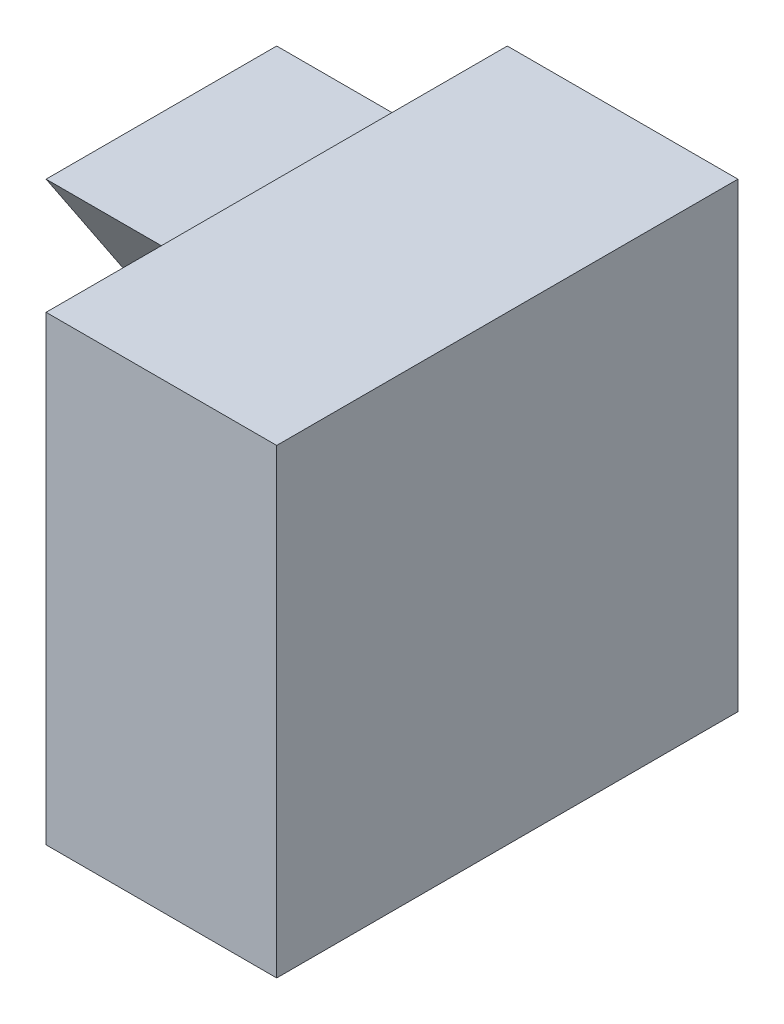
SolidWorks part; units mm, degrees
ref_plane "Front Plane" through (0, 0, 0) normal (0, 0, 1) x (1, 0, 0)
ref_plane "Top Plane" through (0, 0, 0) normal (0, 1, 0) x (1, 0, 0)
ref_plane "Right Plane" through (0, 0, 0) normal (1, 0, 0) x (0, 0, -1)
sketch "Sketch1" plane through (0, 0, 0) normal (1, 0, 0) x (0, 0, -1)
  line L1 (0, 0) -> (4, 0)
  line L2 (0, 0) -> (0, 4)
  line L3 (0, 4) -> (4, 4)
  line L4 (4, 0) -> (4, 4)
  dimension "D1" = 4
  dimension "D2" = 4
extrude "Boss-Extrude1" add sketch "Sketch1" along normal blind 2
sketch "Sketch2" plane through (0, 0, 0) normal (-1, 0, 0) x (0, 0, 1)
  line L1 (-4, 0) -> (-2, 0)
  line L2 (-4, 0) -> (-4, 3)
  line L3 (-4, 3) -> (-2, 3)
  line L4 (-2, 0) -> (-2, 3)
  dimension "D1" = 3
  dimension "D2" = 2
extrude "Boss-Extrude2" add sketch "Sketch2" along normal blind 2
sketch "Sketch3" plane through (-2, 0, 0) normal (-1, 0, 0) x (0, 0, 1)
  line L0 (-2, 3) -> (-4, 0)
  line L1 (-4, 0) -> (-2, 0)
  line L2 (-2, 0) -> (-2, 3)
extrude "Cut-Extrude1" cut sketch "Sketch3" against normal blind 2
